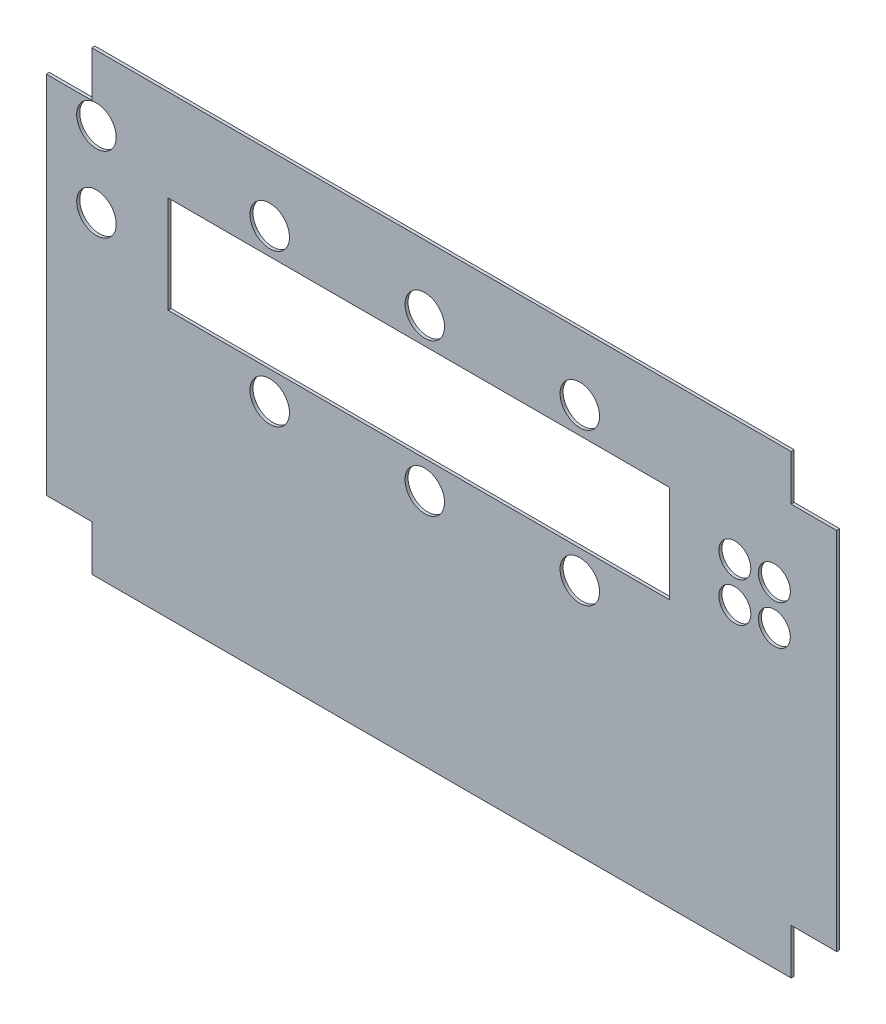
SolidWorks part; units mm, degrees
material "7079 Alloy"
ref_plane "Front" through (0, 0, 0) normal (0, 0, 1) x (1, 0, 0)
ref_plane "Top" through (0, 0, 0) normal (0, 1, 0) x (1, 0, 0)
ref_plane "Right" through (0, 0, 0) normal (1, 0, 0) x (0, 0, -1)
sketch "Sketch1" plane through (0, 0, 0) normal (0, 0, 1) x (1, 0, 0)
  line L0 (142, -87) -> (-142, 87) construction
  line L1 (-115, 75) -> (115, 75)
  line L2 (-130, -60) -> (-130, 60)
  line L3 (-115, -75) -> (115, -75)
  line L4 (130, 60) -> (130, -60)
  line L5 (115, 75) -> (115, 60)
  line L8 (115, 60) -> (130, 60)
  line L9 (0, 48.7465) -> (0, -33.5112) construction
  line L10 (-62.6461, 0) -> (60.1053, 0) construction
  line L11 (115, -60) -> (130, -60)
  line L14 (115, -75) -> (115, -60)
  line L15 (-115, -75) -> (-115, -60)
  line L18 (-130, -60) -> (-115, -60)
  line L19 (-130, 60) -> (-115, 60)
  line L22 (-115, 75) -> (-115, 60)
  dimension "D1" = 15
  dimension "D2" = 15
  dimension "D3" = 260
  dimension "D4" = 150
extrude "Extrude1" add sketch "Sketch1" along normal blind 1
sketch "Sketch2" plane through (0, 0, 1) normal (0, 0, 1) x (1, 0, 0)
  line L0 (115, 75) -> (-115, 75) construction
  line L1 (-90, 44.75) -> (75, 44.75)
  line L2 (-90, 44.75) -> (-90, 12.75)
  line L3 (-90, 12.75) -> (75, 12.75)
  line L4 (75, 44.75) -> (75, 12.75)
  line L5 (130, -60) -> (130, 60) construction
  line L7 (-130, 60) -> (-130, -60) construction
  line L8 (-115, -75) -> (115, -75) construction
  dimension "D1" = 32
  dimension "D2" = 165
  dimension "D3" = 30.25
  dimension "D4" = 55
extrude "Cut-Extrude1" cut sketch "Sketch2" against normal blind 1
sketch "Sketch3" plane through (0, 0, 1) normal (0, 0, 1) x (1, 0, 0)
  line L0 (115, 75) -> (-115, 75) construction
  line L2 (130, -60) -> (130, 60) construction
  line L3 (-90, 44.75) -> (-90, 12.75) construction
  line L4 (75, 12.75) -> (75, 44.75) construction
  circle A0 centre (-113.5, 53.5) radius 6.5
  circle A1 centre (-113.5, 28.75) radius 6.5
  circle A2 centre (-56.5, 3.5) radius 6.5
  circle A3 centre (-5.5, 3.5) radius 6.5
  circle A4 centre (45.5, 3.5) radius 6.5
  circle A5 centre (45.5, 53.5) radius 6.5
  circle A6 centre (-5.5, 53.5) radius 6.5
  circle A7 centre (-56.5, 53.5) radius 6.5
  circle A8 centre (96.5, 35) radius 5.25
  circle A9 centre (109.5, 35) radius 5.25
  circle A10 centre (109.5, 22) radius 5.25
  circle A11 centre (96.5, 22) radius 5.25
  dimension "D1" = 13
  dimension "D2" = 21.5
  dimension "D3" = 24.75
  dimension "D5" = 71.5
  dimension "D6" = 57
  dimension "D7" = 51
  dimension "D8" = 51
  dimension "D9" = 10.5
  dimension "D10" = 13
  dimension "D11" = 20.5
  dimension "D12" = 40
  dimension "D13" = 13
  dimension "D14" = 13
  dimension "D15" = 13
  dimension "D4" = 23.5
  dimension "D16" = 21.5
extrude "Corte-extrusão1" cut sketch "Sketch3" against normal through all
